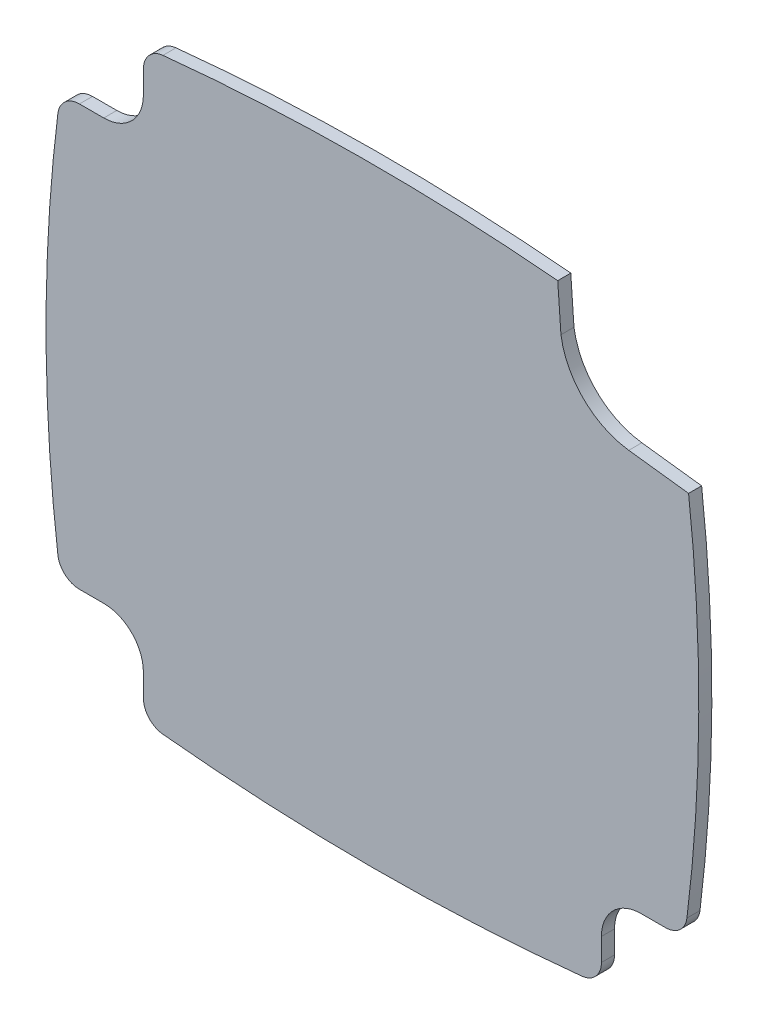
SolidWorks part; units mm, degrees
ref_plane "Front" through (0, 0, 0) normal (0, 0, 1) x (1, 0, 0)
ref_plane "Top" through (0, 0, 0) normal (0, 1, 0) x (1, 0, 0)
ref_plane "Right" through (0, 0, 0) normal (1, 0, 0) x (0, 0, -1)
sketch "Çizim1" plane through (0, 0, 0) normal (0, 0, 1) x (1, 0, 0)
  line L0 (-13.4695, 9.6632) -> (-12.3508, 9.6632)
  line L1 (-10.5305, 12.5213) -> (-10.5305, 11.4835)
  line L2 (-13.4695, -9.6632) -> (-12.3508, -9.6632)
  line L3 (-10.5305, -12.5213) -> (-10.5305, -11.4835)
  line L4 (14.5368, 8.1606) -> (11.7866, 8.5005)
  line L5 (8.6677, 11.5413) -> (8.5208, 13.6226)
  line L6 (10.5305, -12.5213) -> (10.5305, -11.4835)
  line L7 (13.4695, -9.6632) -> (12.3508, -9.6632)
  arc A0 (-9.6318, 13.5161) -> (-10.5305, 12.5213) centre (-9.5305, 12.5213) ccw
  arc A1 (-13.4695, 9.6632) -> (-14.4619, 8.7864) centre (-13.4695, 8.6632) ccw
  arc A2 (-14.4619, -8.7864) -> (-13.4695, -9.6632) centre (-13.4695, -8.6632) ccw
  arc A3 (-10.5305, -12.5213) -> (-9.6318, -13.5161) centre (-9.5305, -12.5213) ccw
  arc A4 (9.6318, -13.5161) -> (10.5305, -12.5213) centre (9.5305, -12.5213) ccw
  arc A5 (13.4695, -9.6632) -> (14.4619, -8.7864) centre (13.4695, -8.6632) ccw
  arc A16 (8.5208, 13.6226) -> (-9.6318, 13.5161) centre (0, -81.0833) ccw
  arc A17 (-12.3508, 9.6632) -> (-10.5305, 11.4835) centre (-12.3508, 11.4835) ccw
  arc A18 (-14.4619, 8.7864) -> (-14.4619, -8.7864) centre (56.3168, 0) ccw
  arc A19 (-10.5305, -11.4835) -> (-12.3508, -9.6632) centre (-12.3508, -11.4835) ccw
  arc A20 (-9.6318, -13.5161) -> (9.6318, -13.5161) centre (0, 81.0833) ccw
  arc A21 (12.3508, -9.6632) -> (10.5305, -11.4835) centre (12.3508, -11.4835) ccw
  arc A22 (14.4619, -8.7864) -> (14.5368, 8.1606) centre (-56.3168, 0) ccw
  arc A23 (8.6677, 11.5413) -> (11.7866, 8.5005) centre (12.2281, 12.0734) ccw
  dimension "D1" = 1
extrude "Yükseklik-Ekstrüzyon1" add sketch "Çizim1" along normal blind 0.6
